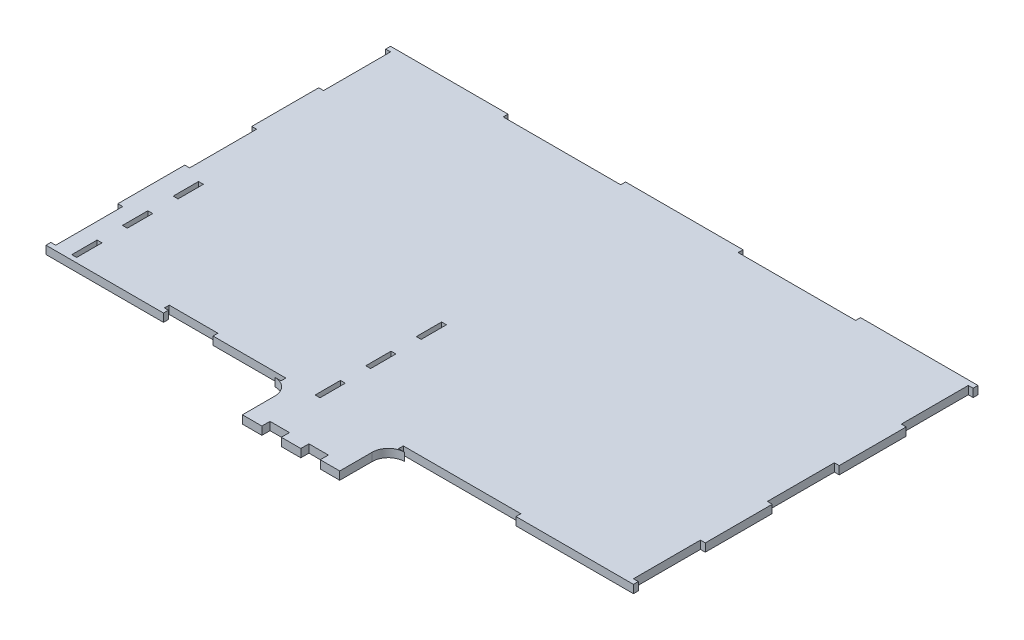
SolidWorks part; units mm, degrees
ref_plane "Front Plane" through (0, 0, 0) normal (0, 0, 1) x (1, 0, 0)
ref_plane "Top Plane" through (0, 0, 0) normal (0, 1, 0) x (1, 0, 0)
ref_plane "Right Plane" through (0, 0, 0) normal (1, 0, 0) x (0, 0, -1)
sketch "Sketch1" plane through (0, 0, 0) normal (0, 1, 0) x (1, 0, 0)
  line L0 (-30, -136.2503) -> (-18, -136.2503)
  line L5 (-181.15, 106.25) -> (181.15, -106.25) construction
  line L6 (-181.15, -106.25) -> (181.15, 106.25) construction
  line L13 (-30, -116.25) -> (-30, -136.2503)
  line L17 (30, -136.2503) -> (30, -116.25)
  line L18 (-18, -131.2503) -> (-6, -131.2503)
  line L20 (18, -136.2503) -> (30, -136.2503)
  line L21 (-6, -136.2503) -> (6, -136.2503)
  line L23 (-18, -136.2503) -> (-18, -131.2503)
  line L24 (-6, -136.2503) -> (-6, -131.2503)
  line L25 (6, -136.2503) -> (6, -131.2503)
  line L26 (18, -136.2503) -> (18, -131.2503)
  line L28 (6, -131.2503) -> (18, -131.2503)
  line L54 (-181.15, 106.25) -> (-181.15, 103.25) construction
  line L55 (181.15, 106.25) -> (108.69, 106.25)
  line L60 (-181.15, -106.25) -> (-181.15, -103.25)
  line L62 (-181.15, 103.25) -> (181.15, 103.25) construction
  line L63 (-108.69, 103.2497) -> (-36.23, 103.2497)
  line L64 (36.23, 106.25) -> (-36.23, 106.25)
  line L65 (36.23, 103.2497) -> (108.69, 103.2497)
  line L66 (-108.69, 103.2497) -> (-108.69, 106.25)
  line L67 (-36.23, 103.2497) -> (-36.23, 106.25)
  line L68 (36.23, 103.2497) -> (36.23, 106.25)
  line L69 (108.69, 103.2497) -> (108.69, 106.25)
  line L70 (-108.69, 106.25) -> (-181.15, 106.25)
  line L71 (-181.15, -103.25) -> (-178.15, -103.25)
  line L72 (-108.69, -106.25) -> (-108.69, -103.25)
  line L73 (-178.15, -103.25) -> (-178.15, -61.95)
  line L74 (-181.15, -61.95) -> (-181.15, -20.65)
  line L75 (-178.15, -20.65) -> (-178.15, 20.65)
  line L76 (-181.15, 20.65) -> (-181.15, 61.95)
  line L77 (-178.15, 61.95) -> (-178.15, 103.25)
  line L78 (-178.15, 61.95) -> (-181.15, 61.95)
  line L79 (-178.15, 20.65) -> (-181.15, 20.65)
  line L80 (-178.15, -20.65) -> (-181.15, -20.65)
  line L81 (-178.15, -61.95) -> (-181.15, -61.95)
  line L82 (-181.15, 103.25) -> (-181.15, 106.25)
  line L83 (-181.15, 103.25) -> (-178.15, 103.25)
  line L84 (-36.23, -106.25) -> (-40, -106.25)
  line L85 (181.15, -103.25) -> (178.15, -103.25)
  line L86 (178.15, -103.25) -> (178.15, -61.95)
  line L87 (178.15, -61.95) -> (181.15, -61.95)
  line L88 (181.15, -61.95) -> (181.15, -20.65)
  line L89 (178.15, -20.65) -> (181.15, -20.65)
  line L90 (178.15, -20.65) -> (178.15, 20.65)
  line L91 (178.15, 20.65) -> (181.15, 20.65)
  line L92 (181.15, 20.65) -> (181.15, 61.95)
  line L93 (178.15, 61.95) -> (181.15, 61.95)
  line L94 (178.15, 61.95) -> (178.15, 103.25)
  line L95 (181.15, 103.25) -> (178.15, 103.25)
  line L96 (181.15, -106.25) -> (181.15, -103.25)
  line L97 (181.15, 103.25) -> (181.15, 106.25)
  line L98 (-181.15, -106.25) -> (-108.69, -106.25)
  line L99 (108.69, -103.2497) -> (108.69, -106.25)
  line L100 (36.23, -103.2497) -> (108.69, -103.2497)
  line L101 (36.23, -103.2497) -> (36.23, -106.25)
  line L102 (40, -106.25) -> (36.23, -106.25)
  line L103 (-36.23, -103.2497) -> (-36.23, -106.25)
  line L106 (108.69, -106.25) -> (181.15, -106.25)
  line L107 (-81.15, -100.25) -> (-111.15, -100.25)
  line L108 (-81.15, -103.2497) -> (-36.23, -103.2497)
  line L109 (-108.69, -103.25) -> (-111.15, -103.25)
  line L110 (-165.15, -103.3556) -> (-168.15, -103.3556)
  line L111 (-81.15, -100.25) -> (-81.15, -103.2497)
  line L112 (-111.15, -100.25) -> (-111.15, -103.25)
  line L113 (-18.15, -103.25) -> (-15.15, -103.25)
  line L114 (-165.15, -25.1796) -> (-165.15, -40.8148)
  line L116 (-168.15, -103.3556) -> (-168.15, -87.7204)
  line L118 (-15.15, -103.25) -> (-15.15, -87.65)
  line L119 (-18.15, -25.25) -> (-18.15, -40.85)
  line L120 (-165.15, -25.1796) -> (-168.15, -25.1796)
  line L121 (-15.15, -25.25) -> (-18.15, -25.25)
  line L123 (-168.15, -72.0852) -> (-168.15, -56.45)
  line L124 (-165.15, -87.7204) -> (-165.15, -103.3556)
  line L125 (-168.15, -40.8148) -> (-168.15, -25.1796)
  line L126 (-168.15, -40.8148) -> (-165.15, -40.8148)
  line L127 (-168.15, -56.45) -> (-165.15, -56.45)
  line L128 (-168.15, -72.0852) -> (-165.15, -72.0852)
  line L129 (-168.15, -87.7204) -> (-165.15, -87.7204)
  line L130 (-165.15, -56.45) -> (-165.15, -72.0852)
  line L131 (-15.15, -72.05) -> (-15.15, -56.45)
  line L132 (-18.15, -87.65) -> (-18.15, -103.25)
  line L133 (-15.15, -40.85) -> (-15.15, -25.25)
  line L134 (-15.15, -40.85) -> (-18.15, -40.85)
  line L135 (-15.15, -56.45) -> (-18.15, -56.45)
  line L136 (-15.15, -72.05) -> (-18.15, -72.05)
  line L137 (-15.15, -87.65) -> (-18.15, -87.65)
  line L138 (-18.15, -56.45) -> (-18.15, -72.05)
  arc A0 (-40, -106.25) -> (-30, -116.25) centre (-40, -116.25) cw
  arc A1 (40, -106.25) -> (30, -116.25) centre (40, -116.25) ccw
  point P0 (0, 0)
  dimension "D3" = 10
  dimension "D4" = 10
  dimension "D1" = 212.5
  dimension "D2" = 153
  dimension "D5" = 78
  dimension "D6" = 3
extrude "Boss-Extrude1" add sketch "Sketch1" along normal blind 5
